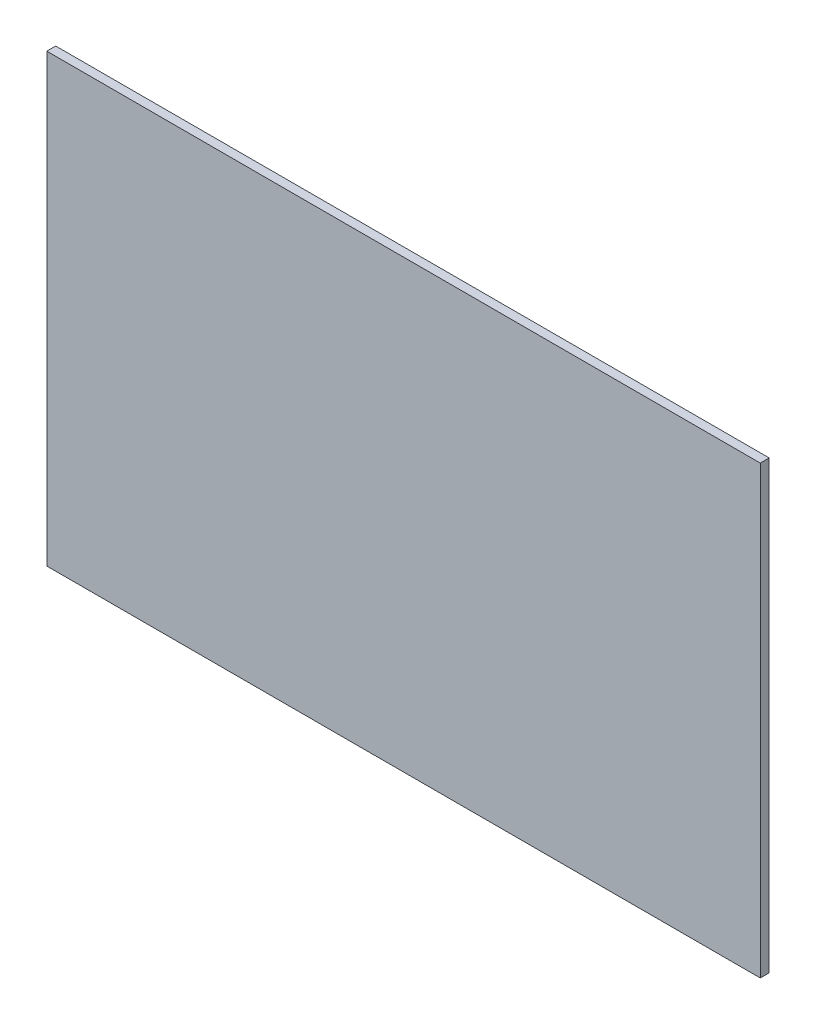
SolidWorks part; units mm, degrees
ref_plane "Front Plane" through (0, 0, 0) normal (0, 0, 1) x (1, 0, 0)
ref_plane "Top Plane" through (0, 0, 0) normal (0, 1, 0) x (1, 0, 0)
ref_plane "Right Plane" through (0, 0, 0) normal (1, 0, 0) x (0, 0, -1)
sketch "Sketch1" plane through (0, 0, 0) normal (0, 0, 1) x (1, 0, 0)
  line L1 (-400, 250) -> (400, 250)
  line L2 (-400, 250) -> (-400, -250)
  line L3 (-400, -250) -> (400, -250)
  line L4 (400, 250) -> (400, -250)
  line L5 (-400, 250) -> (400, -250) construction
  line L6 (-400, -250) -> (400, 250) construction
  point P0 (0, 0)
  dimension "D1" = 800
  dimension "D2" = 500
extrude "Boss-Extrude1" add sketch "Sketch1" along normal blind 10
